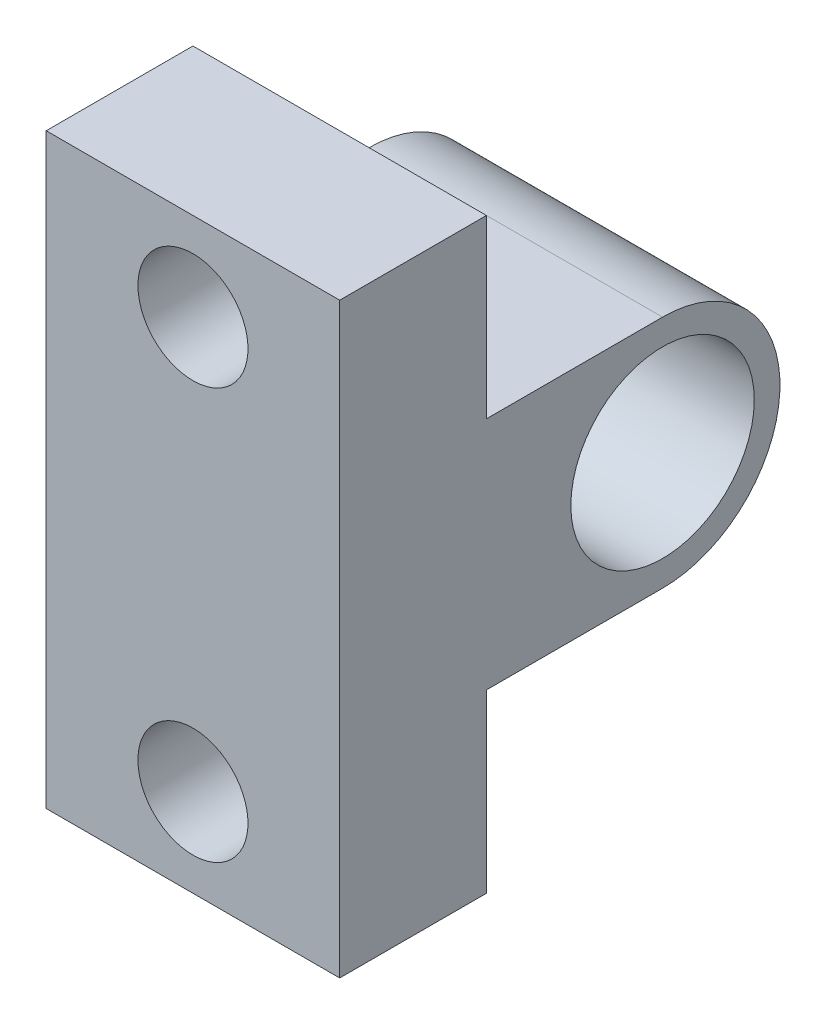
SolidWorks part; units mm, degrees
ref_plane "Front Plane" through (0, 0, 0) normal (0, 0, 1) x (1, 0, 0)
ref_plane "Top Plane" through (0, 0, 0) normal (0, 1, 0) x (1, 0, 0)
ref_plane "Right Plane" through (0, 0, 0) normal (1, 0, 0) x (0, 0, -1)
sketch "Sketch1" plane through (0, 0, 0) normal (1, 0, 0) x (0, 0, -1)
  line L0 (-26.5871, 4.995) -> (-26.5871, -2.625)
  line L1 (-18.9671, 15.155) -> (-26.5871, 15.155)
  line L3 (-18.9671, 4.995) -> (-26.5871, 4.995)
  line L5 (-26.5871, 22.775) -> (-32.9371, 22.775)
  line L6 (-26.5871, 22.775) -> (-26.5871, 15.155)
  line L7 (-26.5871, -2.625) -> (-32.9371, -2.625)
  line L8 (-32.9371, 22.775) -> (-32.9371, -2.625)
  circle A0 centre (-18.9671, 10.075) radius 3.9688
  arc A1 (-18.9671, 4.995) -> (-18.9671, 15.155) centre (-18.9671, 10.075) ccw
  dimension "D1" = 7.62
  dimension "D4" = 7.9375
  dimension "D5" = 6.35
  dimension "D2" = 25.4
  dimension "D3" = 7.62
extrude "Boss-Extrude1" add sketch "Sketch1" along normal blind 12.7
sketch "Sketch2" plane through (0, 0, 26.5871) normal (0, 0, -1) x (-1, 0, 0)
  line L0 (0, 15.155) -> (0, 22.775) construction
  line L1 (-12.7, 22.775) -> (0, 22.775) construction
  circle A0 centre (-6.35, 18.965) radius 2.3813
  circle A1 centre (-6.35, 1.185) radius 2.3813
  point P2 (-6.35, 18.965)
  point P5 (0, 18.965)
  dimension "D3" = 4.7625
  dimension "D1" = 6.35
  dimension "D2" = 3.81
  dimension "D5" = 17.78
  dimension "D4" = 2
extrude "Cut-Extrude1" cut sketch "Sketch2" against normal through all
